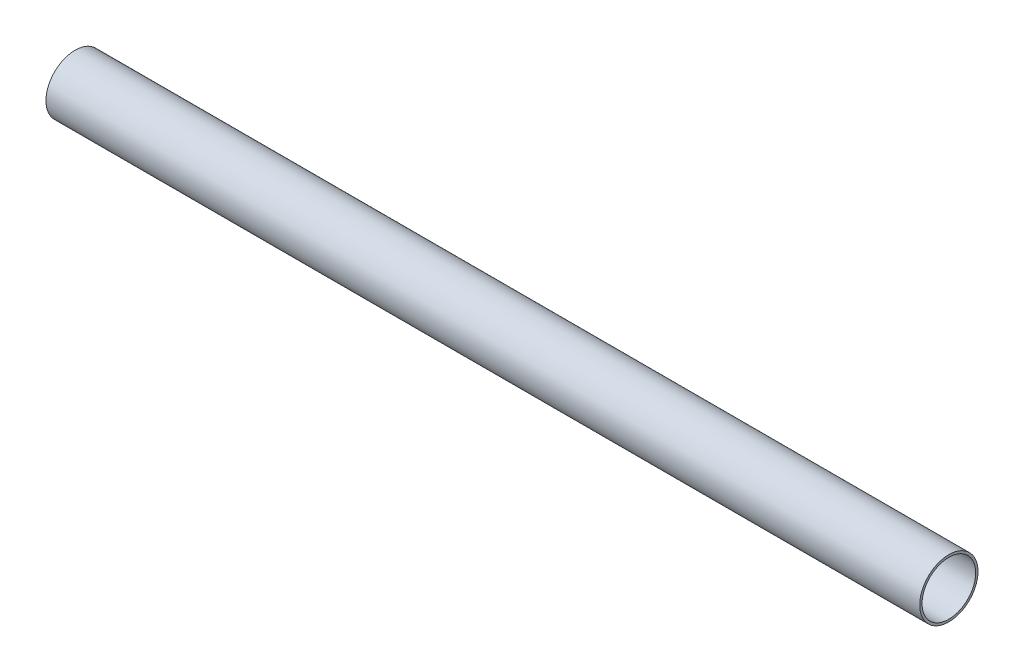
SolidWorks part; units mm, degrees
material "Plain Carbon Steel"
ref_plane "Front Plane" through (0, 0, 0) normal (0, 0, 1) x (1, 0, 0)
ref_plane "Top Plane" through (0, 0, 0) normal (0, 1, 0) x (1, 0, 0)
ref_plane "Right Plane" through (0, 0, 0) normal (1, 0, 0) x (0, 0, -1)
sketch "Sketch1" plane through (0, 0, 0) normal (1, 0, 0) x (0, 0, -1)
  circle A0 centre (0, 0) radius 25
  circle A1 centre (0, 0) radius 23
  dimension "D1" = 50
  dimension "D2" = 2
extrude "Boss-Extrude1" add sketch "Sketch1" along normal blind 749.3
